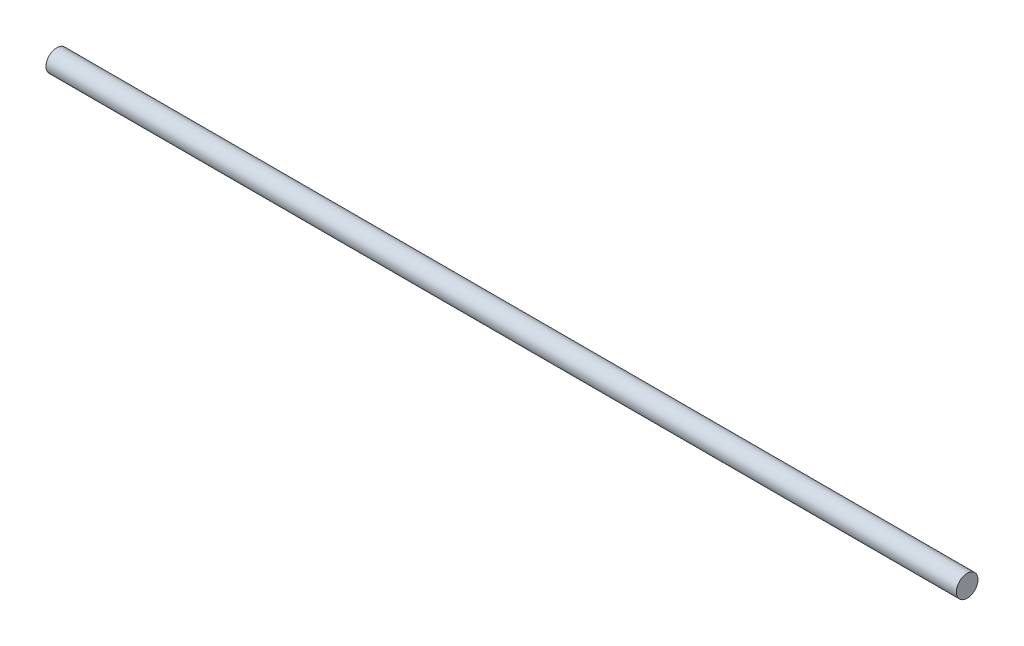
SolidWorks part; units mm, degrees
ref_plane "Ön Düzlem" through (0, 0, 0) normal (0, 0, 1) x (1, 0, 0)
ref_plane "Üst Düzlem" through (0, 0, 0) normal (0, 1, 0) x (1, 0, 0)
ref_plane "Sağ Düzlem" through (0, 0, 0) normal (1, 0, 0) x (0, 0, -1)
sketch "Sketch1" plane through (0, 0, 0) normal (0, 0, 1) x (1, 0, 0)
  line L1 (-63, 0.75) -> (63, 0.75)
  line L2 (-63, 0.75) -> (-63, -0.75)
  line L3 (-63, -0.75) -> (63, -0.75)
  line L4 (63, 0.75) -> (63, -0.75)
  line L5 (-63, 0.75) -> (63, -0.75) construction
  line L6 (-63, -0.75) -> (63, 0.75) construction
  point P0 (0, 0)
  dimension "D1" = 126
  dimension "D2" = 1.5
revolve "Revolve1" add sketch "Sketch1" angle 360 about L3
